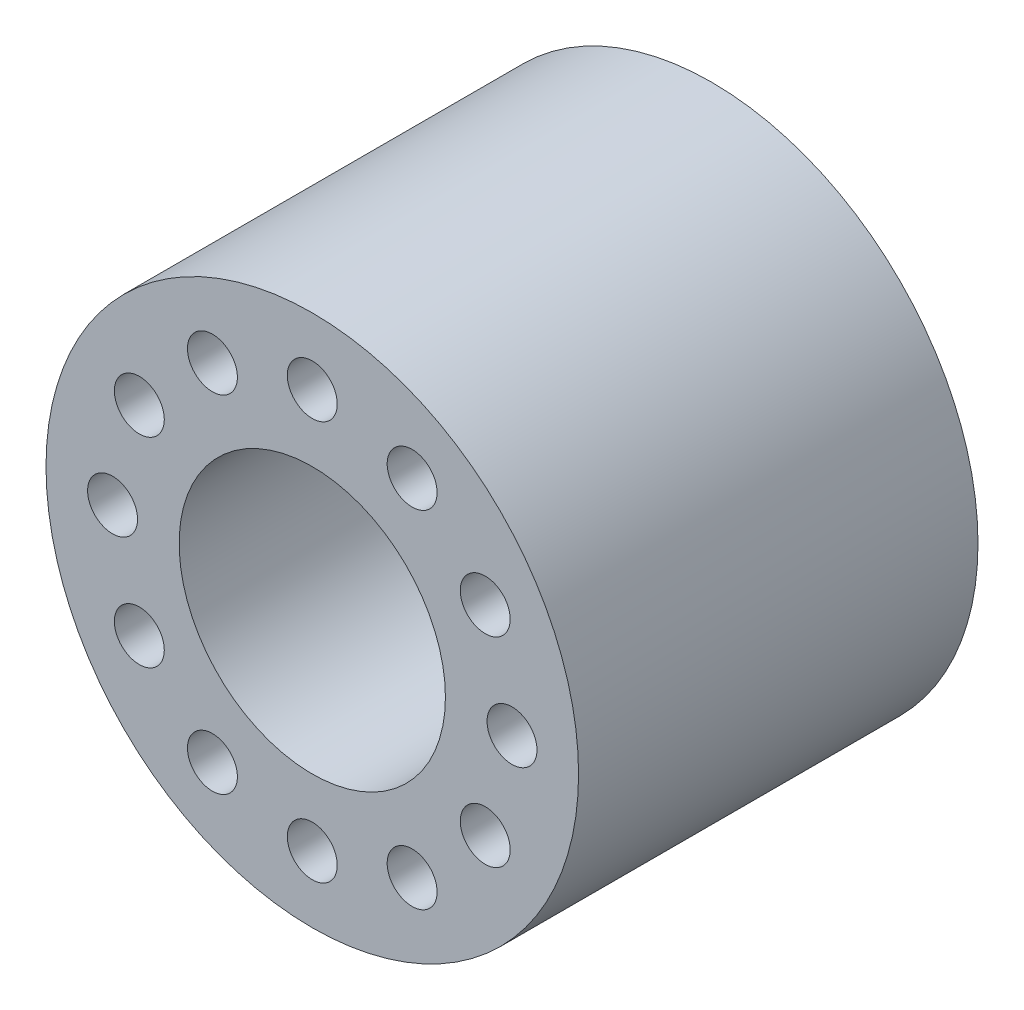
SolidWorks part; units mm, degrees
ref_plane "前视基准面" through (0, 0, 0) normal (0, 0, 1) x (1, 0, 0)
ref_plane "上视基准面" through (0, 0, 0) normal (0, 1, 0) x (1, 0, 0)
ref_plane "右视基准面" through (0, 0, 0) normal (1, 0, 0) x (0, 0, -1)
sketch "草图1" plane through (0, 0, 0) normal (0, 0, 1) x (1, 0, 0)
  line L0 (0, 0) -> (6, 0) construction
  line L1 (5.1962, 3) -> (0, 0) construction
  circle A0 centre (6, 0) radius 0.75
  circle A1 centre (5.1962, -3) radius 0.75
  circle A2 centre (3, -5.1962) radius 0.75
  circle A3 centre (0, -6) radius 0.75
  circle A4 centre (-3, -5.1962) radius 0.75
  circle A5 centre (-5.1962, -3) radius 0.75
  circle A6 centre (-6, 0) radius 0.75
  circle A7 centre (-5.1962, 3) radius 0.75
  circle A8 centre (-3, 5.1962) radius 0.75
  circle A9 centre (0, 6) radius 0.75
  circle A10 centre (3, 5.1962) radius 0.75
  circle A11 centre (5.1962, 3) radius 0.75
  circle A12 centre (0, 0) radius 8
  circle A13 centre (0, 0) radius 4
  point P26 (0, 0)
  dimension "D1" = 1.5
  dimension "D2" = 6
  dimension "D3" = 12
  dimension "D5" = 30
  dimension "D6" = 6
  dimension "D4" = 16
  dimension "D7" = 8
extrude "凸台-拉伸1" add sketch "草图1" along normal blind 12
